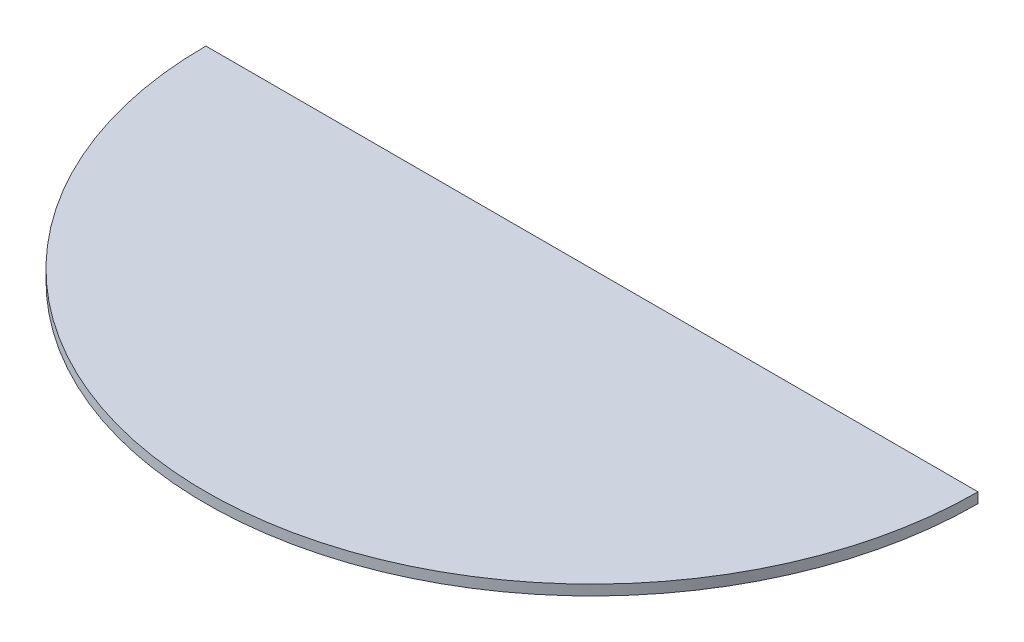
SolidWorks part; units mm, degrees
ref_plane "Front Plane" through (0, 0, 0) normal (0, 0, 1) x (1, 0, 0)
ref_plane "Top Plane" through (0, 0, 0) normal (0, 1, 0) x (1, 0, 0)
ref_plane "Right Plane" through (0, 0, 0) normal (1, 0, 0) x (0, 0, -1)
sketch "Sketch1" plane through (0, 0, 0) normal (0, 1, 0) x (1, 0, 0)
  line L0 (-75, 0) -> (75, 0)
  arc A0 (-75, 0) -> (75, 0) centre (0, 0) ccw
  dimension "D1" = 75
  dimension "D2" = 150
extrude "Boss-Extrude1" add sketch "Sketch1" along normal mid plane 2
